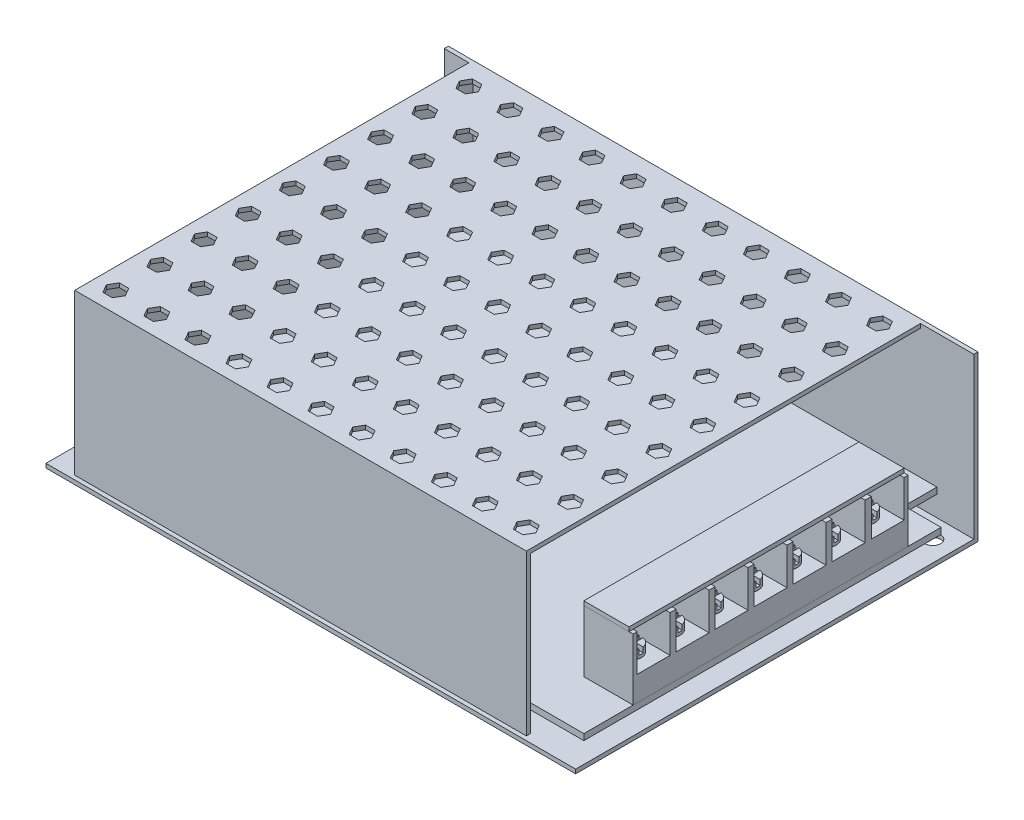
SolidWorks part; units mm, degrees
ref_plane "Front Plane" through (0, 0, 0) normal (0, 0, 1) x (1, 0, 0)
ref_plane "Top Plane" through (0, 0, 0) normal (0, 1, 0) x (1, 0, 0)
ref_plane "Right Plane" through (0, 0, 0) normal (1, 0, 0) x (0, 0, -1)
sketch "Sketch1" plane through (0, 0, 0) normal (0, 1, 0) x (1, 0, 0)
  line L1 (-64.5, -49) -> (64.5, -49)
  line L2 (-64.5, -49) -> (-64.5, 49)
  line L3 (-64.5, 49) -> (64.5, 49)
  line L4 (64.5, -49) -> (64.5, 49)
  line L5 (-64.5, -49) -> (64.5, 49) construction
  line L6 (-64.5, 49) -> (64.5, -49) construction
  point P0 (0, 0)
  dimension "D1" = 129
  dimension "D2" = 98
extrude "Boss-Extrude1" add sketch "Sketch1" along normal blind 1
sketch "Sketch2" plane through (0, 1, 0) normal (0, 1, 0) x (1, 0, 0)
  line L0 (64.5, -49) -> (64.5, 49) construction
  line L1 (-64.5, 49) -> (64.5, 49)
  line L2 (-64.5, 49) -> (-64.5, 48)
  line L3 (-64.5, 48) -> (-58.5, 48)
  line L4 (64.5, 49) -> (64.5, 48)
  line L6 (-58.5, -48) -> (51.5, -48)
  line L7 (-58.5, -48) -> (-58.5, -47)
  line L8 (-57.5, -47) -> (51.5, -47)
  line L9 (51.5, -48) -> (51.5, -47)
  line L10 (-64.5, -49) -> (64.5, -49) construction
  line L11 (-64.5, 49) -> (-64.5, -49) construction
  line L12 (-57.5, 48) -> (64.5, 48)
  line L14 (-58.5, -47) -> (-58.5, 48)
  line L16 (-57.5, -47) -> (-57.5, 48)
  dimension "D1" = 1
  dimension "D2" = 1
  dimension "D3" = 13
  dimension "D4" = 6
  dimension "D5" = 1
extrude "Boss-Extrude2" add sketch "Sketch2" along normal blind 39
sketch "Sketch4" plane through (0, 0, 47) normal (0, 0, -1) x (-1, 0, 0)
  line L0 (58.5, 40) -> (58.5, 1) construction
  line L1 (-51.5, 40) -> (58.5, 40)
  line L2 (-51.5, 40) -> (-51.5, 39)
  line L3 (-51.5, 39) -> (58.5, 39)
  line L4 (58.5, 40) -> (58.5, 39)
  dimension "D1" = 1
extrude "Boss-Extrude3" add sketch "Sketch4" along normal up to surface (95 mm away) up to face at (-61.5, 20.5, -48)
sketch "Sketch5" plane through (0, 40, 0) normal (0, 1, 0) x (1, 0, 0)
  line L0 (-58.5, 48) -> (51.5, 48) construction
  line L1 (-64.5, 48) -> (-58.5, 48) construction
  line L2 (51.5, -48) -> (51.5, 48) construction
  line L3 (-58.5, 48) -> (-58.5, -48) construction
  line L4 (-51.1906, 43) -> (-52.3453, 45)
  line L5 (-52.3453, 45) -> (-54.6547, 45)
  line L6 (-54.6547, 45) -> (-55.8094, 43)
  line L7 (-55.8094, 43) -> (-54.6547, 41)
  line L8 (-54.6547, 41) -> (-52.3453, 41)
  line L9 (-52.3453, 41) -> (-51.1906, 43)
  line L10 (48.8094, 43) -> (44.1906, 43) construction
  line L11 (-41.1906, 43) -> (-42.3453, 45)
  line L12 (-42.3453, 45) -> (-44.6547, 45)
  line L13 (-44.6547, 45) -> (-45.8094, 43)
  line L14 (-45.8094, 43) -> (-44.6547, 41)
  line L15 (-44.6547, 41) -> (-42.3453, 41)
  line L16 (-42.3453, 41) -> (-41.1906, 43)
  line L17 (-31.1906, 43) -> (-32.3453, 45)
  line L18 (-32.3453, 45) -> (-34.6547, 45)
  line L19 (-34.6547, 45) -> (-35.8094, 43)
  line L20 (-35.8094, 43) -> (-34.6547, 41)
  line L21 (-34.6547, 41) -> (-32.3453, 41)
  line L22 (-32.3453, 41) -> (-31.1906, 43)
  line L23 (-21.1906, 43) -> (-22.3453, 45)
  line L24 (-22.3453, 45) -> (-24.6547, 45)
  line L25 (-24.6547, 45) -> (-25.8094, 43)
  line L26 (-25.8094, 43) -> (-24.6547, 41)
  line L27 (-24.6547, 41) -> (-22.3453, 41)
  line L28 (-22.3453, 41) -> (-21.1906, 43)
  line L29 (-11.1906, 43) -> (-12.3453, 45)
  line L30 (-12.3453, 45) -> (-14.6547, 45)
  line L31 (-14.6547, 45) -> (-15.8094, 43)
  line L32 (-15.8094, 43) -> (-14.6547, 41)
  line L33 (-14.6547, 41) -> (-12.3453, 41)
  line L34 (-12.3453, 41) -> (-11.1906, 43)
  line L35 (-1.1906, 43) -> (-2.3453, 45)
  line L36 (-2.3453, 45) -> (-4.6547, 45)
  line L37 (-4.6547, 45) -> (-5.8094, 43)
  line L38 (-5.8094, 43) -> (-4.6547, 41)
  line L39 (-4.6547, 41) -> (-2.3453, 41)
  line L40 (-2.3453, 41) -> (-1.1906, 43)
  line L41 (8.8094, 43) -> (7.6547, 45)
  line L42 (7.6547, 45) -> (5.3453, 45)
  line L43 (5.3453, 45) -> (4.1906, 43)
  line L44 (4.1906, 43) -> (5.3453, 41)
  line L45 (5.3453, 41) -> (7.6547, 41)
  line L46 (7.6547, 41) -> (8.8094, 43)
  line L47 (18.8094, 43) -> (17.6547, 45)
  line L48 (17.6547, 45) -> (15.3453, 45)
  line L49 (15.3453, 45) -> (14.1906, 43)
  line L50 (14.1906, 43) -> (15.3453, 41)
  line L51 (15.3453, 41) -> (17.6547, 41)
  line L52 (17.6547, 41) -> (18.8094, 43)
  line L53 (28.8094, 43) -> (27.6547, 45)
  line L54 (27.6547, 45) -> (25.3453, 45)
  line L55 (25.3453, 45) -> (24.1906, 43)
  line L56 (24.1906, 43) -> (25.3453, 41)
  line L57 (25.3453, 41) -> (27.6547, 41)
  line L58 (27.6547, 41) -> (28.8094, 43)
  line L59 (38.8094, 43) -> (37.6547, 45)
  line L60 (37.6547, 45) -> (35.3453, 45)
  line L61 (35.3453, 45) -> (34.1906, 43)
  line L62 (34.1906, 43) -> (35.3453, 41)
  line L63 (35.3453, 41) -> (37.6547, 41)
  line L64 (37.6547, 41) -> (38.8094, 43)
  line L65 (48.8094, 43) -> (47.6547, 45)
  line L66 (47.6547, 45) -> (45.3453, 45)
  line L67 (45.3453, 45) -> (44.1906, 43)
  line L68 (44.1906, 43) -> (45.3453, 41)
  line L69 (45.3453, 41) -> (47.6547, 41)
  line L70 (47.6547, 41) -> (48.8094, 43)
  line L71 (-41.1906, 32.25) -> (-42.3453, 34.25)
  line L72 (-42.3453, 34.25) -> (-44.6547, 34.25)
  line L73 (-44.6547, 34.25) -> (-45.8094, 32.25)
  line L74 (-45.8094, 32.25) -> (-44.6547, 30.25)
  line L75 (-44.6547, 30.25) -> (-42.3453, 30.25)
  line L76 (-42.3453, 30.25) -> (-41.1906, 32.25)
  line L77 (-31.1906, 32.25) -> (-32.3453, 34.25)
  line L78 (-32.3453, 34.25) -> (-34.6547, 34.25)
  line L79 (-34.6547, 34.25) -> (-35.8094, 32.25)
  line L80 (-35.8094, 32.25) -> (-34.6547, 30.25)
  line L81 (-34.6547, 30.25) -> (-32.3453, 30.25)
  line L82 (-32.3453, 30.25) -> (-31.1906, 32.25)
  line L83 (-21.1906, 32.25) -> (-22.3453, 34.25)
  line L84 (-22.3453, 34.25) -> (-24.6547, 34.25)
  line L85 (-24.6547, 34.25) -> (-25.8094, 32.25)
  line L86 (-25.8094, 32.25) -> (-24.6547, 30.25)
  line L87 (-24.6547, 30.25) -> (-22.3453, 30.25)
  line L88 (-22.3453, 30.25) -> (-21.1906, 32.25)
  line L89 (-11.1906, 32.25) -> (-12.3453, 34.25)
  line L90 (-12.3453, 34.25) -> (-14.6547, 34.25)
  line L91 (-14.6547, 34.25) -> (-15.8094, 32.25)
  line L92 (-15.8094, 32.25) -> (-14.6547, 30.25)
  line L93 (-14.6547, 30.25) -> (-12.3453, 30.25)
  line L94 (-12.3453, 30.25) -> (-11.1906, 32.25)
  line L95 (-1.1906, 32.25) -> (-2.3453, 34.25)
  line L96 (-2.3453, 34.25) -> (-4.6547, 34.25)
  line L97 (-4.6547, 34.25) -> (-5.8094, 32.25)
  line L98 (-5.8094, 32.25) -> (-4.6547, 30.25)
  line L99 (-4.6547, 30.25) -> (-2.3453, 30.25)
  line L100 (-2.3453, 30.25) -> (-1.1906, 32.25)
  line L101 (8.8094, 32.25) -> (7.6547, 34.25)
  line L102 (7.6547, 34.25) -> (5.3453, 34.25)
  line L103 (5.3453, 34.25) -> (4.1906, 32.25)
  line L104 (4.1906, 32.25) -> (5.3453, 30.25)
  line L105 (5.3453, 30.25) -> (7.6547, 30.25)
  line L106 (7.6547, 30.25) -> (8.8094, 32.25)
  line L107 (18.8094, 32.25) -> (17.6547, 34.25)
  line L108 (17.6547, 34.25) -> (15.3453, 34.25)
  line L109 (15.3453, 34.25) -> (14.1906, 32.25)
  line L110 (14.1906, 32.25) -> (15.3453, 30.25)
  line L111 (15.3453, 30.25) -> (17.6547, 30.25)
  line L112 (17.6547, 30.25) -> (18.8094, 32.25)
  line L113 (28.8094, 32.25) -> (27.6547, 34.25)
  line L114 (27.6547, 34.25) -> (25.3453, 34.25)
  line L115 (25.3453, 34.25) -> (24.1906, 32.25)
  line L116 (24.1906, 32.25) -> (25.3453, 30.25)
  line L117 (25.3453, 30.25) -> (27.6547, 30.25)
  line L118 (27.6547, 30.25) -> (28.8094, 32.25)
  line L119 (38.8094, 32.25) -> (37.6547, 34.25)
  line L120 (37.6547, 34.25) -> (35.3453, 34.25)
  line L121 (35.3453, 34.25) -> (34.1906, 32.25)
  line L122 (34.1906, 32.25) -> (35.3453, 30.25)
  line L123 (35.3453, 30.25) -> (37.6547, 30.25)
  line L124 (37.6547, 30.25) -> (38.8094, 32.25)
  line L125 (48.8094, 32.25) -> (47.6547, 34.25)
  line L126 (47.6547, 34.25) -> (45.3453, 34.25)
  line L127 (45.3453, 34.25) -> (44.1906, 32.25)
  line L128 (44.1906, 32.25) -> (45.3453, 30.25)
  line L129 (45.3453, 30.25) -> (47.6547, 30.25)
  line L130 (47.6547, 30.25) -> (48.8094, 32.25)
  line L131 (-41.1906, 21.5) -> (-42.3453, 23.5)
  line L132 (-42.3453, 23.5) -> (-44.6547, 23.5)
  line L133 (-44.6547, 23.5) -> (-45.8094, 21.5)
  line L134 (-45.8094, 21.5) -> (-44.6547, 19.5)
  line L135 (-44.6547, 19.5) -> (-42.3453, 19.5)
  line L136 (-42.3453, 19.5) -> (-41.1906, 21.5)
  line L137 (-31.1906, 21.5) -> (-32.3453, 23.5)
  line L138 (-32.3453, 23.5) -> (-34.6547, 23.5)
  line L139 (-34.6547, 23.5) -> (-35.8094, 21.5)
  line L140 (-35.8094, 21.5) -> (-34.6547, 19.5)
  line L141 (-34.6547, 19.5) -> (-32.3453, 19.5)
  line L142 (-32.3453, 19.5) -> (-31.1906, 21.5)
  line L143 (-21.1906, 21.5) -> (-22.3453, 23.5)
  line L144 (-22.3453, 23.5) -> (-24.6547, 23.5)
  line L145 (-24.6547, 23.5) -> (-25.8094, 21.5)
  line L146 (-25.8094, 21.5) -> (-24.6547, 19.5)
  line L147 (-24.6547, 19.5) -> (-22.3453, 19.5)
  line L148 (-22.3453, 19.5) -> (-21.1906, 21.5)
  line L149 (-11.1906, 21.5) -> (-12.3453, 23.5)
  line L150 (-12.3453, 23.5) -> (-14.6547, 23.5)
  line L151 (-14.6547, 23.5) -> (-15.8094, 21.5)
  line L152 (-15.8094, 21.5) -> (-14.6547, 19.5)
  line L153 (-14.6547, 19.5) -> (-12.3453, 19.5)
  line L154 (-12.3453, 19.5) -> (-11.1906, 21.5)
  line L155 (-1.1906, 21.5) -> (-2.3453, 23.5)
  line L156 (-2.3453, 23.5) -> (-4.6547, 23.5)
  line L157 (-4.6547, 23.5) -> (-5.8094, 21.5)
  line L158 (-5.8094, 21.5) -> (-4.6547, 19.5)
  line L159 (-4.6547, 19.5) -> (-2.3453, 19.5)
  line L160 (-2.3453, 19.5) -> (-1.1906, 21.5)
  line L161 (8.8094, 21.5) -> (7.6547, 23.5)
  line L162 (7.6547, 23.5) -> (5.3453, 23.5)
  line L163 (5.3453, 23.5) -> (4.1906, 21.5)
  line L164 (4.1906, 21.5) -> (5.3453, 19.5)
  line L165 (5.3453, 19.5) -> (7.6547, 19.5)
  line L166 (7.6547, 19.5) -> (8.8094, 21.5)
  line L167 (18.8094, 21.5) -> (17.6547, 23.5)
  line L168 (17.6547, 23.5) -> (15.3453, 23.5)
  line L169 (15.3453, 23.5) -> (14.1906, 21.5)
  line L170 (14.1906, 21.5) -> (15.3453, 19.5)
  line L171 (15.3453, 19.5) -> (17.6547, 19.5)
  line L172 (17.6547, 19.5) -> (18.8094, 21.5)
  line L173 (28.8094, 21.5) -> (27.6547, 23.5)
  line L174 (27.6547, 23.5) -> (25.3453, 23.5)
  line L175 (25.3453, 23.5) -> (24.1906, 21.5)
  line L176 (24.1906, 21.5) -> (25.3453, 19.5)
  line L177 (25.3453, 19.5) -> (27.6547, 19.5)
  line L178 (27.6547, 19.5) -> (28.8094, 21.5)
  line L179 (38.8094, 21.5) -> (37.6547, 23.5)
  line L180 (37.6547, 23.5) -> (35.3453, 23.5)
  line L181 (35.3453, 23.5) -> (34.1906, 21.5)
  line L182 (34.1906, 21.5) -> (35.3453, 19.5)
  line L183 (35.3453, 19.5) -> (37.6547, 19.5)
  line L184 (37.6547, 19.5) -> (38.8094, 21.5)
  line L185 (48.8094, 21.5) -> (47.6547, 23.5)
  line L186 (47.6547, 23.5) -> (45.3453, 23.5)
  line L187 (45.3453, 23.5) -> (44.1906, 21.5)
  line L188 (44.1906, 21.5) -> (45.3453, 19.5)
  line L189 (45.3453, 19.5) -> (47.6547, 19.5)
  line L190 (47.6547, 19.5) -> (48.8094, 21.5)
  line L191 (-41.1906, 10.75) -> (-42.3453, 12.75)
  line L192 (-42.3453, 12.75) -> (-44.6547, 12.75)
  line L193 (-44.6547, 12.75) -> (-45.8094, 10.75)
  line L194 (-45.8094, 10.75) -> (-44.6547, 8.75)
  line L195 (-44.6547, 8.75) -> (-42.3453, 8.75)
  line L196 (-42.3453, 8.75) -> (-41.1906, 10.75)
  line L197 (-31.1906, 10.75) -> (-32.3453, 12.75)
  line L198 (-32.3453, 12.75) -> (-34.6547, 12.75)
  line L199 (-34.6547, 12.75) -> (-35.8094, 10.75)
  line L200 (-35.8094, 10.75) -> (-34.6547, 8.75)
  line L201 (-34.6547, 8.75) -> (-32.3453, 8.75)
  line L202 (-32.3453, 8.75) -> (-31.1906, 10.75)
  line L203 (-21.1906, 10.75) -> (-22.3453, 12.75)
  line L204 (-22.3453, 12.75) -> (-24.6547, 12.75)
  line L205 (-24.6547, 12.75) -> (-25.8094, 10.75)
  line L206 (-25.8094, 10.75) -> (-24.6547, 8.75)
  line L207 (-24.6547, 8.75) -> (-22.3453, 8.75)
  line L208 (-22.3453, 8.75) -> (-21.1906, 10.75)
  line L209 (-11.1906, 10.75) -> (-12.3453, 12.75)
  line L210 (-12.3453, 12.75) -> (-14.6547, 12.75)
  line L211 (-14.6547, 12.75) -> (-15.8094, 10.75)
  line L212 (-15.8094, 10.75) -> (-14.6547, 8.75)
  line L213 (-14.6547, 8.75) -> (-12.3453, 8.75)
  line L214 (-12.3453, 8.75) -> (-11.1906, 10.75)
  line L215 (-1.1906, 10.75) -> (-2.3453, 12.75)
  line L216 (-2.3453, 12.75) -> (-4.6547, 12.75)
  line L217 (-4.6547, 12.75) -> (-5.8094, 10.75)
  line L218 (-5.8094, 10.75) -> (-4.6547, 8.75)
  line L219 (-4.6547, 8.75) -> (-2.3453, 8.75)
  line L220 (-2.3453, 8.75) -> (-1.1906, 10.75)
  line L221 (8.8094, 10.75) -> (7.6547, 12.75)
  line L222 (7.6547, 12.75) -> (5.3453, 12.75)
  line L223 (5.3453, 12.75) -> (4.1906, 10.75)
  line L224 (4.1906, 10.75) -> (5.3453, 8.75)
  line L225 (5.3453, 8.75) -> (7.6547, 8.75)
  line L226 (7.6547, 8.75) -> (8.8094, 10.75)
  line L227 (18.8094, 10.75) -> (17.6547, 12.75)
  line L228 (17.6547, 12.75) -> (15.3453, 12.75)
  line L229 (15.3453, 12.75) -> (14.1906, 10.75)
  line L230 (14.1906, 10.75) -> (15.3453, 8.75)
  line L231 (15.3453, 8.75) -> (17.6547, 8.75)
  line L232 (17.6547, 8.75) -> (18.8094, 10.75)
  line L233 (28.8094, 10.75) -> (27.6547, 12.75)
  line L234 (27.6547, 12.75) -> (25.3453, 12.75)
  line L235 (25.3453, 12.75) -> (24.1906, 10.75)
  line L236 (24.1906, 10.75) -> (25.3453, 8.75)
  line L237 (25.3453, 8.75) -> (27.6547, 8.75)
  line L238 (27.6547, 8.75) -> (28.8094, 10.75)
  line L239 (38.8094, 10.75) -> (37.6547, 12.75)
  line L240 (37.6547, 12.75) -> (35.3453, 12.75)
  line L241 (35.3453, 12.75) -> (34.1906, 10.75)
  line L242 (34.1906, 10.75) -> (35.3453, 8.75)
  line L243 (35.3453, 8.75) -> (37.6547, 8.75)
  line L244 (37.6547, 8.75) -> (38.8094, 10.75)
  line L245 (48.8094, 10.75) -> (47.6547, 12.75)
  line L246 (47.6547, 12.75) -> (45.3453, 12.75)
  line L247 (45.3453, 12.75) -> (44.1906, 10.75)
  line L248 (44.1906, 10.75) -> (45.3453, 8.75)
  line L249 (45.3453, 8.75) -> (47.6547, 8.75)
  line L250 (47.6547, 8.75) -> (48.8094, 10.75)
  line L251 (-41.1906, 0) -> (-42.3453, 2)
  line L252 (-42.3453, 2) -> (-44.6547, 2)
  line L253 (-44.6547, 2) -> (-45.8094, 0)
  line L254 (-45.8094, 0) -> (-44.6547, -2)
  line L255 (-44.6547, -2) -> (-42.3453, -2)
  line L256 (-42.3453, -2) -> (-41.1906, 0)
  line L257 (-31.1906, 0) -> (-32.3453, 2)
  line L258 (-32.3453, 2) -> (-34.6547, 2)
  line L259 (-34.6547, 2) -> (-35.8094, 0)
  line L260 (-35.8094, 0) -> (-34.6547, -2)
  line L261 (-34.6547, -2) -> (-32.3453, -2)
  line L262 (-32.3453, -2) -> (-31.1906, 0)
  line L263 (-21.1906, 0) -> (-22.3453, 2)
  line L264 (-22.3453, 2) -> (-24.6547, 2)
  line L265 (-24.6547, 2) -> (-25.8094, 0)
  line L266 (-25.8094, 0) -> (-24.6547, -2)
  line L267 (-24.6547, -2) -> (-22.3453, -2)
  line L268 (-22.3453, -2) -> (-21.1906, 0)
  line L269 (-11.1906, 0) -> (-12.3453, 2)
  line L270 (-12.3453, 2) -> (-14.6547, 2)
  line L271 (-14.6547, 2) -> (-15.8094, 0)
  line L272 (-15.8094, 0) -> (-14.6547, -2)
  line L273 (-14.6547, -2) -> (-12.3453, -2)
  line L274 (-12.3453, -2) -> (-11.1906, 0)
  line L275 (-1.1906, 0) -> (-2.3453, 2)
  line L276 (-2.3453, 2) -> (-4.6547, 2)
  line L277 (-4.6547, 2) -> (-5.8094, 0)
  line L278 (-5.8094, 0) -> (-4.6547, -2)
  line L279 (-4.6547, -2) -> (-2.3453, -2)
  line L280 (-2.3453, -2) -> (-1.1906, 0)
  line L281 (8.8094, 0) -> (7.6547, 2)
  line L282 (7.6547, 2) -> (5.3453, 2)
  line L283 (5.3453, 2) -> (4.1906, 0)
  line L284 (4.1906, 0) -> (5.3453, -2)
  line L285 (5.3453, -2) -> (7.6547, -2)
  line L286 (7.6547, -2) -> (8.8094, 0)
  line L287 (18.8094, 0) -> (17.6547, 2)
  line L288 (17.6547, 2) -> (15.3453, 2)
  line L289 (15.3453, 2) -> (14.1906, 0)
  line L290 (14.1906, 0) -> (15.3453, -2)
  line L291 (15.3453, -2) -> (17.6547, -2)
  line L292 (17.6547, -2) -> (18.8094, 0)
  line L293 (28.8094, 0) -> (27.6547, 2)
  line L294 (27.6547, 2) -> (25.3453, 2)
  line L295 (25.3453, 2) -> (24.1906, 0)
  line L296 (24.1906, 0) -> (25.3453, -2)
  line L297 (25.3453, -2) -> (27.6547, -2)
  line L298 (27.6547, -2) -> (28.8094, 0)
  line L299 (38.8094, 0) -> (37.6547, 2)
  line L300 (37.6547, 2) -> (35.3453, 2)
  line L301 (35.3453, 2) -> (34.1906, 0)
  line L302 (34.1906, 0) -> (35.3453, -2)
  line L303 (35.3453, -2) -> (37.6547, -2)
  line L304 (37.6547, -2) -> (38.8094, 0)
  line L305 (48.8094, 0) -> (47.6547, 2)
  line L306 (47.6547, 2) -> (45.3453, 2)
  line L307 (45.3453, 2) -> (44.1906, 0)
  line L308 (44.1906, 0) -> (45.3453, -2)
  line L309 (45.3453, -2) -> (47.6547, -2)
  line L310 (47.6547, -2) -> (48.8094, 0)
  line L311 (-41.1906, -10.75) -> (-42.3453, -8.75)
  line L312 (-42.3453, -8.75) -> (-44.6547, -8.75)
  line L313 (-44.6547, -8.75) -> (-45.8094, -10.75)
  line L314 (-45.8094, -10.75) -> (-44.6547, -12.75)
  line L315 (-44.6547, -12.75) -> (-42.3453, -12.75)
  line L316 (-42.3453, -12.75) -> (-41.1906, -10.75)
  line L317 (-31.1906, -10.75) -> (-32.3453, -8.75)
  line L318 (-32.3453, -8.75) -> (-34.6547, -8.75)
  line L319 (-34.6547, -8.75) -> (-35.8094, -10.75)
  line L320 (-35.8094, -10.75) -> (-34.6547, -12.75)
  line L321 (-34.6547, -12.75) -> (-32.3453, -12.75)
  line L322 (-32.3453, -12.75) -> (-31.1906, -10.75)
  line L323 (-21.1906, -10.75) -> (-22.3453, -8.75)
  line L324 (-22.3453, -8.75) -> (-24.6547, -8.75)
  line L325 (-24.6547, -8.75) -> (-25.8094, -10.75)
  line L326 (-25.8094, -10.75) -> (-24.6547, -12.75)
  line L327 (-24.6547, -12.75) -> (-22.3453, -12.75)
  line L328 (-22.3453, -12.75) -> (-21.1906, -10.75)
  line L329 (-11.1906, -10.75) -> (-12.3453, -8.75)
  line L330 (-12.3453, -8.75) -> (-14.6547, -8.75)
  line L331 (-14.6547, -8.75) -> (-15.8094, -10.75)
  line L332 (-15.8094, -10.75) -> (-14.6547, -12.75)
  line L333 (-14.6547, -12.75) -> (-12.3453, -12.75)
  line L334 (-12.3453, -12.75) -> (-11.1906, -10.75)
  line L335 (-1.1906, -10.75) -> (-2.3453, -8.75)
  line L336 (-2.3453, -8.75) -> (-4.6547, -8.75)
  line L337 (-4.6547, -8.75) -> (-5.8094, -10.75)
  line L338 (-5.8094, -10.75) -> (-4.6547, -12.75)
  line L339 (-4.6547, -12.75) -> (-2.3453, -12.75)
  line L340 (-2.3453, -12.75) -> (-1.1906, -10.75)
  line L341 (8.8094, -10.75) -> (7.6547, -8.75)
  line L342 (7.6547, -8.75) -> (5.3453, -8.75)
  line L343 (5.3453, -8.75) -> (4.1906, -10.75)
  line L344 (4.1906, -10.75) -> (5.3453, -12.75)
  line L345 (5.3453, -12.75) -> (7.6547, -12.75)
  line L346 (7.6547, -12.75) -> (8.8094, -10.75)
  line L347 (18.8094, -10.75) -> (17.6547, -8.75)
  line L348 (17.6547, -8.75) -> (15.3453, -8.75)
  line L349 (15.3453, -8.75) -> (14.1906, -10.75)
  line L350 (14.1906, -10.75) -> (15.3453, -12.75)
  line L351 (15.3453, -12.75) -> (17.6547, -12.75)
  line L352 (17.6547, -12.75) -> (18.8094, -10.75)
  line L353 (28.8094, -10.75) -> (27.6547, -8.75)
  line L354 (27.6547, -8.75) -> (25.3453, -8.75)
  line L355 (25.3453, -8.75) -> (24.1906, -10.75)
  line L356 (24.1906, -10.75) -> (25.3453, -12.75)
  line L357 (25.3453, -12.75) -> (27.6547, -12.75)
  line L358 (27.6547, -12.75) -> (28.8094, -10.75)
  line L359 (38.8094, -10.75) -> (37.6547, -8.75)
  line L360 (37.6547, -8.75) -> (35.3453, -8.75)
  line L361 (35.3453, -8.75) -> (34.1906, -10.75)
  line L362 (34.1906, -10.75) -> (35.3453, -12.75)
  line L363 (35.3453, -12.75) -> (37.6547, -12.75)
  line L364 (37.6547, -12.75) -> (38.8094, -10.75)
  line L365 (48.8094, -10.75) -> (47.6547, -8.75)
  line L366 (47.6547, -8.75) -> (45.3453, -8.75)
  line L367 (45.3453, -8.75) -> (44.1906, -10.75)
  line L368 (44.1906, -10.75) -> (45.3453, -12.75)
  line L369 (45.3453, -12.75) -> (47.6547, -12.75)
  line L370 (47.6547, -12.75) -> (48.8094, -10.75)
  line L371 (-41.1906, -21.5) -> (-42.3453, -19.5)
  line L372 (-42.3453, -19.5) -> (-44.6547, -19.5)
  line L373 (-44.6547, -19.5) -> (-45.8094, -21.5)
  line L374 (-45.8094, -21.5) -> (-44.6547, -23.5)
  line L375 (-44.6547, -23.5) -> (-42.3453, -23.5)
  line L376 (-42.3453, -23.5) -> (-41.1906, -21.5)
  line L377 (-31.1906, -21.5) -> (-32.3453, -19.5)
  line L378 (-32.3453, -19.5) -> (-34.6547, -19.5)
  line L379 (-34.6547, -19.5) -> (-35.8094, -21.5)
  line L380 (-35.8094, -21.5) -> (-34.6547, -23.5)
  line L381 (-34.6547, -23.5) -> (-32.3453, -23.5)
  line L382 (-32.3453, -23.5) -> (-31.1906, -21.5)
  line L383 (-21.1906, -21.5) -> (-22.3453, -19.5)
  line L384 (-22.3453, -19.5) -> (-24.6547, -19.5)
  line L385 (-24.6547, -19.5) -> (-25.8094, -21.5)
  line L386 (-25.8094, -21.5) -> (-24.6547, -23.5)
  line L387 (-24.6547, -23.5) -> (-22.3453, -23.5)
  line L388 (-22.3453, -23.5) -> (-21.1906, -21.5)
  line L389 (-11.1906, -21.5) -> (-12.3453, -19.5)
  line L390 (-12.3453, -19.5) -> (-14.6547, -19.5)
  line L391 (-14.6547, -19.5) -> (-15.8094, -21.5)
  line L392 (-15.8094, -21.5) -> (-14.6547, -23.5)
  line L393 (-14.6547, -23.5) -> (-12.3453, -23.5)
  line L394 (-12.3453, -23.5) -> (-11.1906, -21.5)
  line L395 (-1.1906, -21.5) -> (-2.3453, -19.5)
  line L396 (-2.3453, -19.5) -> (-4.6547, -19.5)
  line L397 (-4.6547, -19.5) -> (-5.8094, -21.5)
  line L398 (-5.8094, -21.5) -> (-4.6547, -23.5)
  line L399 (-4.6547, -23.5) -> (-2.3453, -23.5)
  line L400 (-2.3453, -23.5) -> (-1.1906, -21.5)
  line L401 (8.8094, -21.5) -> (7.6547, -19.5)
  line L402 (7.6547, -19.5) -> (5.3453, -19.5)
  line L403 (5.3453, -19.5) -> (4.1906, -21.5)
  line L404 (4.1906, -21.5) -> (5.3453, -23.5)
  line L405 (5.3453, -23.5) -> (7.6547, -23.5)
  line L406 (7.6547, -23.5) -> (8.8094, -21.5)
  line L407 (18.8094, -21.5) -> (17.6547, -19.5)
  line L408 (17.6547, -19.5) -> (15.3453, -19.5)
  line L409 (15.3453, -19.5) -> (14.1906, -21.5)
  line L410 (14.1906, -21.5) -> (15.3453, -23.5)
  line L411 (15.3453, -23.5) -> (17.6547, -23.5)
  line L412 (17.6547, -23.5) -> (18.8094, -21.5)
  line L413 (28.8094, -21.5) -> (27.6547, -19.5)
  line L414 (27.6547, -19.5) -> (25.3453, -19.5)
  line L415 (25.3453, -19.5) -> (24.1906, -21.5)
  line L416 (24.1906, -21.5) -> (25.3453, -23.5)
  line L417 (25.3453, -23.5) -> (27.6547, -23.5)
  line L418 (27.6547, -23.5) -> (28.8094, -21.5)
  line L419 (38.8094, -21.5) -> (37.6547, -19.5)
  line L420 (37.6547, -19.5) -> (35.3453, -19.5)
  line L421 (35.3453, -19.5) -> (34.1906, -21.5)
  line L422 (34.1906, -21.5) -> (35.3453, -23.5)
  line L423 (35.3453, -23.5) -> (37.6547, -23.5)
  line L424 (37.6547, -23.5) -> (38.8094, -21.5)
  line L425 (48.8094, -21.5) -> (47.6547, -19.5)
  line L426 (47.6547, -19.5) -> (45.3453, -19.5)
  line L427 (45.3453, -19.5) -> (44.1906, -21.5)
  line L428 (44.1906, -21.5) -> (45.3453, -23.5)
  line L429 (45.3453, -23.5) -> (47.6547, -23.5)
  line L430 (47.6547, -23.5) -> (48.8094, -21.5)
  line L431 (-41.1906, -32.25) -> (-42.3453, -30.25)
  line L432 (-42.3453, -30.25) -> (-44.6547, -30.25)
  line L433 (-44.6547, -30.25) -> (-45.8094, -32.25)
  line L434 (-45.8094, -32.25) -> (-44.6547, -34.25)
  line L435 (-44.6547, -34.25) -> (-42.3453, -34.25)
  line L436 (-42.3453, -34.25) -> (-41.1906, -32.25)
  line L437 (-31.1906, -32.25) -> (-32.3453, -30.25)
  line L438 (-32.3453, -30.25) -> (-34.6547, -30.25)
  line L439 (-34.6547, -30.25) -> (-35.8094, -32.25)
  line L440 (-35.8094, -32.25) -> (-34.6547, -34.25)
  line L441 (-34.6547, -34.25) -> (-32.3453, -34.25)
  line L442 (-32.3453, -34.25) -> (-31.1906, -32.25)
  line L443 (-21.1906, -32.25) -> (-22.3453, -30.25)
  line L444 (-22.3453, -30.25) -> (-24.6547, -30.25)
  line L445 (-24.6547, -30.25) -> (-25.8094, -32.25)
  line L446 (-25.8094, -32.25) -> (-24.6547, -34.25)
  line L447 (-24.6547, -34.25) -> (-22.3453, -34.25)
  line L448 (-22.3453, -34.25) -> (-21.1906, -32.25)
  line L449 (-11.1906, -32.25) -> (-12.3453, -30.25)
  line L450 (-12.3453, -30.25) -> (-14.6547, -30.25)
  line L451 (-14.6547, -30.25) -> (-15.8094, -32.25)
  line L452 (-15.8094, -32.25) -> (-14.6547, -34.25)
  line L453 (-14.6547, -34.25) -> (-12.3453, -34.25)
  line L454 (-12.3453, -34.25) -> (-11.1906, -32.25)
  line L455 (-1.1906, -32.25) -> (-2.3453, -30.25)
  line L456 (-2.3453, -30.25) -> (-4.6547, -30.25)
  line L457 (-4.6547, -30.25) -> (-5.8094, -32.25)
  line L458 (-5.8094, -32.25) -> (-4.6547, -34.25)
  line L459 (-4.6547, -34.25) -> (-2.3453, -34.25)
  line L460 (-2.3453, -34.25) -> (-1.1906, -32.25)
  line L461 (8.8094, -32.25) -> (7.6547, -30.25)
  line L462 (7.6547, -30.25) -> (5.3453, -30.25)
  line L463 (5.3453, -30.25) -> (4.1906, -32.25)
  line L464 (4.1906, -32.25) -> (5.3453, -34.25)
  line L465 (5.3453, -34.25) -> (7.6547, -34.25)
  line L466 (7.6547, -34.25) -> (8.8094, -32.25)
  line L467 (18.8094, -32.25) -> (17.6547, -30.25)
  line L468 (17.6547, -30.25) -> (15.3453, -30.25)
  line L469 (15.3453, -30.25) -> (14.1906, -32.25)
  line L470 (14.1906, -32.25) -> (15.3453, -34.25)
  line L471 (15.3453, -34.25) -> (17.6547, -34.25)
  line L472 (17.6547, -34.25) -> (18.8094, -32.25)
  line L473 (28.8094, -32.25) -> (27.6547, -30.25)
  line L474 (27.6547, -30.25) -> (25.3453, -30.25)
  line L475 (25.3453, -30.25) -> (24.1906, -32.25)
  line L476 (24.1906, -32.25) -> (25.3453, -34.25)
  line L477 (25.3453, -34.25) -> (27.6547, -34.25)
  line L478 (27.6547, -34.25) -> (28.8094, -32.25)
  line L479 (38.8094, -32.25) -> (37.6547, -30.25)
  line L480 (37.6547, -30.25) -> (35.3453, -30.25)
  line L481 (35.3453, -30.25) -> (34.1906, -32.25)
  line L482 (34.1906, -32.25) -> (35.3453, -34.25)
  line L483 (35.3453, -34.25) -> (37.6547, -34.25)
  line L484 (37.6547, -34.25) -> (38.8094, -32.25)
  line L485 (48.8094, -32.25) -> (47.6547, -30.25)
  line L486 (47.6547, -30.25) -> (45.3453, -30.25)
  line L487 (45.3453, -30.25) -> (44.1906, -32.25)
  line L488 (44.1906, -32.25) -> (45.3453, -34.25)
  line L489 (45.3453, -34.25) -> (47.6547, -34.25)
  line L490 (47.6547, -34.25) -> (48.8094, -32.25)
  line L491 (-41.1906, -43) -> (-42.3453, -41)
  line L492 (-42.3453, -41) -> (-44.6547, -41)
  line L493 (-44.6547, -41) -> (-45.8094, -43)
  line L494 (-45.8094, -43) -> (-44.6547, -45)
  line L495 (-44.6547, -45) -> (-42.3453, -45)
  line L496 (-42.3453, -45) -> (-41.1906, -43)
  line L497 (-31.1906, -43) -> (-32.3453, -41)
  line L498 (-32.3453, -41) -> (-34.6547, -41)
  line L499 (-34.6547, -41) -> (-35.8094, -43)
  line L500 (-35.8094, -43) -> (-34.6547, -45)
  line L501 (-34.6547, -45) -> (-32.3453, -45)
  line L502 (-32.3453, -45) -> (-31.1906, -43)
  line L503 (-21.1906, -43) -> (-22.3453, -41)
  line L504 (-22.3453, -41) -> (-24.6547, -41)
  line L505 (-24.6547, -41) -> (-25.8094, -43)
  line L506 (-25.8094, -43) -> (-24.6547, -45)
  line L507 (-24.6547, -45) -> (-22.3453, -45)
  line L508 (-22.3453, -45) -> (-21.1906, -43)
  line L509 (-11.1906, -43) -> (-12.3453, -41)
  line L510 (-12.3453, -41) -> (-14.6547, -41)
  line L511 (-14.6547, -41) -> (-15.8094, -43)
  line L512 (-15.8094, -43) -> (-14.6547, -45)
  line L513 (-14.6547, -45) -> (-12.3453, -45)
  line L514 (-12.3453, -45) -> (-11.1906, -43)
  line L515 (-1.1906, -43) -> (-2.3453, -41)
  line L516 (-2.3453, -41) -> (-4.6547, -41)
  line L517 (-4.6547, -41) -> (-5.8094, -43)
  line L518 (-5.8094, -43) -> (-4.6547, -45)
  line L519 (-4.6547, -45) -> (-2.3453, -45)
  line L520 (-2.3453, -45) -> (-1.1906, -43)
  line L521 (8.8094, -43) -> (7.6547, -41)
  line L522 (7.6547, -41) -> (5.3453, -41)
  line L523 (5.3453, -41) -> (4.1906, -43)
  line L524 (4.1906, -43) -> (5.3453, -45)
  line L525 (5.3453, -45) -> (7.6547, -45)
  line L526 (7.6547, -45) -> (8.8094, -43)
  line L527 (18.8094, -43) -> (17.6547, -41)
  line L528 (17.6547, -41) -> (15.3453, -41)
  line L529 (15.3453, -41) -> (14.1906, -43)
  line L530 (14.1906, -43) -> (15.3453, -45)
  line L531 (15.3453, -45) -> (17.6547, -45)
  line L532 (17.6547, -45) -> (18.8094, -43)
  line L533 (28.8094, -43) -> (27.6547, -41)
  line L534 (27.6547, -41) -> (25.3453, -41)
  line L535 (25.3453, -41) -> (24.1906, -43)
  line L536 (24.1906, -43) -> (25.3453, -45)
  line L537 (25.3453, -45) -> (27.6547, -45)
  line L538 (27.6547, -45) -> (28.8094, -43)
  line L539 (38.8094, -43) -> (37.6547, -41)
  line L540 (37.6547, -41) -> (35.3453, -41)
  line L541 (35.3453, -41) -> (34.1906, -43)
  line L542 (34.1906, -43) -> (35.3453, -45)
  line L543 (35.3453, -45) -> (37.6547, -45)
  line L544 (37.6547, -45) -> (38.8094, -43)
  line L545 (48.8094, -43) -> (47.6547, -41)
  line L546 (47.6547, -41) -> (45.3453, -41)
  line L547 (45.3453, -41) -> (44.1906, -43)
  line L548 (44.1906, -43) -> (45.3453, -45)
  line L549 (45.3453, -45) -> (47.6547, -45)
  line L550 (47.6547, -45) -> (48.8094, -43)
  line L551 (-51.1906, 32.25) -> (-52.3453, 34.25)
  line L552 (-52.3453, 34.25) -> (-54.6547, 34.25)
  line L553 (-54.6547, 34.25) -> (-55.8094, 32.25)
  line L554 (-55.8094, 32.25) -> (-54.6547, 30.25)
  line L555 (-54.6547, 30.25) -> (-52.3453, 30.25)
  line L556 (-52.3453, 30.25) -> (-51.1906, 32.25)
  line L557 (-51.1906, 21.5) -> (-52.3453, 23.5)
  line L558 (-52.3453, 23.5) -> (-54.6547, 23.5)
  line L559 (-54.6547, 23.5) -> (-55.8094, 21.5)
  line L560 (-55.8094, 21.5) -> (-54.6547, 19.5)
  line L561 (-54.6547, 19.5) -> (-52.3453, 19.5)
  line L562 (-52.3453, 19.5) -> (-51.1906, 21.5)
  line L563 (-51.1906, 10.75) -> (-52.3453, 12.75)
  line L564 (-52.3453, 12.75) -> (-54.6547, 12.75)
  line L565 (-54.6547, 12.75) -> (-55.8094, 10.75)
  line L566 (-55.8094, 10.75) -> (-54.6547, 8.75)
  line L567 (-54.6547, 8.75) -> (-52.3453, 8.75)
  line L568 (-52.3453, 8.75) -> (-51.1906, 10.75)
  line L569 (-51.1906, 0) -> (-52.3453, 2)
  line L570 (-52.3453, 2) -> (-54.6547, 2)
  line L571 (-54.6547, 2) -> (-55.8094, 0)
  line L572 (-55.8094, 0) -> (-54.6547, -2)
  line L573 (-54.6547, -2) -> (-52.3453, -2)
  line L574 (-52.3453, -2) -> (-51.1906, 0)
  line L575 (-51.1906, -10.75) -> (-52.3453, -8.75)
  line L576 (-52.3453, -8.75) -> (-54.6547, -8.75)
  line L577 (-54.6547, -8.75) -> (-55.8094, -10.75)
  line L578 (-55.8094, -10.75) -> (-54.6547, -12.75)
  line L579 (-54.6547, -12.75) -> (-52.3453, -12.75)
  line L580 (-52.3453, -12.75) -> (-51.1906, -10.75)
  line L581 (-51.1906, -21.5) -> (-52.3453, -19.5)
  line L582 (-52.3453, -19.5) -> (-54.6547, -19.5)
  line L583 (-54.6547, -19.5) -> (-55.8094, -21.5)
  line L584 (-55.8094, -21.5) -> (-54.6547, -23.5)
  line L585 (-54.6547, -23.5) -> (-52.3453, -23.5)
  line L586 (-52.3453, -23.5) -> (-51.1906, -21.5)
  line L587 (-51.1906, -32.25) -> (-52.3453, -30.25)
  line L588 (-52.3453, -30.25) -> (-54.6547, -30.25)
  line L589 (-54.6547, -30.25) -> (-55.8094, -32.25)
  line L590 (-55.8094, -32.25) -> (-54.6547, -34.25)
  line L591 (-54.6547, -34.25) -> (-52.3453, -34.25)
  line L592 (-52.3453, -34.25) -> (-51.1906, -32.25)
  line L593 (-51.1906, -43) -> (-52.3453, -41)
  line L594 (-52.3453, -41) -> (-54.6547, -41)
  line L595 (-54.6547, -41) -> (-55.8094, -43)
  line L596 (-55.8094, -43) -> (-54.6547, -45)
  line L597 (-54.6547, -45) -> (-52.3453, -45)
  line L598 (-52.3453, -45) -> (-51.1906, -43)
  line L599 (-53.5, -45) -> (-53.5, -41) construction
  line L600 (-58.5, -48) -> (51.5, -48) construction
  circle A0 centre (-53.5, 43) radius 2 construction
  point P16 (-53.5, -43)
  point P19 (46.5, 43)
  dimension "D3" = 4
  dimension "D1" = 5
  dimension "D2" = 5
  dimension "D6" = 5
  dimension "D7" = 5
  dimension "D4" = 11
  dimension "D5" = 9
extrude "Cut-Extrude1" cut sketch "Sketch5" against normal up to next (1 mm away)
ref_plane "Plane1" through (0, 6, 0) normal (0, 1, 0) x (1, 0, 0)
sketch "Sketch7" plane through (0, 6, 0) normal (0, 1, 0) x (1, 0, 0)
  line L0 (55.5, 48) -> (55.5, 40)
  line L1 (-57.5, -47) -> (64.5, -47)
  line L2 (-57.5, -47) -> (-57.5, 48)
  line L3 (-57.5, 48) -> (55.5, 48)
  line L4 (64.5, -47) -> (64.5, 40)
  line L5 (55.5, 40) -> (64.5, 40)
  line L6 (64.5, -49) -> (64.5, 48) construction
  line L7 (-64.5, 48) -> (-58.5, 48) construction
  dimension "D1" = 8
  dimension "D2" = 9
extrude "Boss-Extrude4" add sketch "Sketch7" along normal blind 1.5 separate body
sketch "Sketch8" plane through (0, 7.5, 0) normal (0, 1, 0) x (1, 0, 0)
  line L0 (64.5, -47) -> (64.5, 40) construction
  line L1 (64.5, -35) -> (52.5, -35)
  line L2 (64.5, -35) -> (64.5, 32)
  line L3 (64.5, 32) -> (52.5, 32)
  line L4 (52.5, -35) -> (52.5, 32)
  line L5 (-57.5, -47) -> (64.5, -47) construction
  line L6 (-64.5, 48) -> (-58.5, 48) construction
  dimension "D1" = 12
  dimension "D2" = 16
  dimension "D3" = 12
extrude "Boss-Extrude5" add sketch "Sketch8" along normal blind 15 separate body
sketch "Sketch9" plane through (0, 22.5, 0) normal (0, 1, 0) x (1, 0, 0)
  line L0 (64.5, -35) -> (64.5, 32) construction
  line L1 (64.5, -34) -> (53.5, -34)
  line L2 (64.5, -34) -> (64.5, -26)
  line L3 (64.5, -26) -> (53.5, -26)
  line L4 (53.5, -34) -> (53.5, -26)
  line L5 (52.5, -35) -> (64.5, -35) construction
  line L6 (52.5, 32) -> (52.5, -35) construction
  line L7 (64.5, -24.5) -> (64.5, -16.5)
  line L8 (64.5, -24.5) -> (53.5, -24.5)
  line L9 (53.5, -24.5) -> (53.5, -16.5)
  line L10 (64.5, -16.5) -> (53.5, -16.5)
  line L11 (64.5, -15) -> (64.5, -7)
  line L12 (64.5, -15) -> (53.5, -15)
  line L13 (53.5, -15) -> (53.5, -7)
  line L14 (64.5, -7) -> (53.5, -7)
  line L15 (64.5, -5.5) -> (64.5, 2.5)
  line L16 (64.5, -5.5) -> (53.5, -5.5)
  line L17 (53.5, -5.5) -> (53.5, 2.5)
  line L18 (64.5, 2.5) -> (53.5, 2.5)
  line L19 (64.5, 4) -> (64.5, 12)
  line L20 (64.5, 4) -> (53.5, 4)
  line L21 (53.5, 4) -> (53.5, 12)
  line L22 (64.5, 12) -> (53.5, 12)
  line L23 (64.5, 13.5) -> (64.5, 21.5)
  line L24 (64.5, 13.5) -> (53.5, 13.5)
  line L25 (53.5, 13.5) -> (53.5, 21.5)
  line L26 (64.5, 21.5) -> (53.5, 21.5)
  line L27 (64.5, 23) -> (64.5, 31)
  line L28 (64.5, 23) -> (53.5, 23)
  line L29 (53.5, 23) -> (53.5, 31)
  line L30 (64.5, 31) -> (53.5, 31)
  line L31 (64.5, 32) -> (52.5, 32) construction
  dimension "D1" = 1
  dimension "D2" = 1
  dimension "D3" = 8
  dimension "D5" = 1
  dimension "D4" = 7
extrude "Cut-Extrude2" cut sketch "Sketch9" against normal offset from surface (9 mm away) 6 up to face at (20.8333, 7.5, -13.6667)
sketch "Sketch10" plane through (0, 13.5, 0) normal (0, 1, 0) x (1, 0, 0)
  line L0 (64.5, -34) -> (64.5, -26) construction
  line L3 (64.5, -30) -> (53.5, -30) construction
  line L4 (53.5, -26) -> (53.5, -34) construction
  circle A0 centre (59, -30) radius 2.5
  point P8 (59, -30)
  dimension "D1" = 5
extrude "Boss-Extrude6" add sketch "Sketch10" along normal blind 2 separate body
sketch "Sketch11" plane through (0, 15.5, 0) normal (0, 1, 0) x (1, 0, 0)
  line L0 (62.4976, -29.5) -> (62.4976, -30.5)
  line L1 (59.5, -33.1667) -> (58.5, -33.1667)
  line L2 (58.5, -26.6938) -> (58.5, -29.5)
  line L3 (62.4976, -29.5) -> (59.5, -29.5)
  line L4 (59.5, -26.6938) -> (59.5, -29.5)
  line L5 (62.4976, -30.5) -> (59.5, -30.5)
  line L6 (55.5775, -30.5) -> (55.5775, -29.5)
  line L7 (58.5, -26.6938) -> (59.5, -26.6938)
  line L8 (58.5, -29.5) -> (55.5775, -29.5)
  line L9 (58.5, -30.5) -> (55.5775, -30.5)
  line L10 (58.5, -30.5) -> (58.5, -33.1667)
  line L11 (59.5, -30.5) -> (59.5, -33.1667)
extrude "Cut-Extrude3" cut sketch "Sketch11" against normal blind 1.25
pattern_linear "LPattern4" count 7 spacing 9.4939 along (0, 0, -1) of "Cut-Extrude3", "Boss-Extrude6"
sketch "Sketch12" plane through (0, 22.5, 0) normal (0, 1, 0) x (1, 0, 0)
  line L0 (64.5, 32) -> (52.5, 32) construction
  line L1 (52.5, -35) -> (63.5, -35)
  line L2 (52.5, -35) -> (52.5, 32)
  line L3 (52.5, 32) -> (63.5, 32)
  line L4 (63.5, -35) -> (63.5, 32)
  line L5 (64.5, 23) -> (64.5, 31) construction
  dimension "D1" = 1
extrude "Boss-Extrude7" add sketch "Sketch12" along normal blind 1 separate body
sketch "Sketch13" plane through (0, 1, 0) normal (0, 1, 0) x (1, 0, 0)
  line L0 (64.5, 49) -> (-64.5, 49) construction
  line L1 (64.5, -49) -> (64.5, 48) construction
  circle A0 centre (59.5, 43) radius 1.9
  dimension "D1" = 3.8
  dimension "D2" = 6
  dimension "D3" = 5
extrude "Cut-Extrude4" cut sketch "Sketch13" against normal through all
equation "\"D2@Sketch2\"=\"D1@Sketch2\""
equation "\"D2@Sketch5\"=\"D1@Sketch5\""
equation "\"D6@Sketch5\"=\"D1@Sketch5\""
